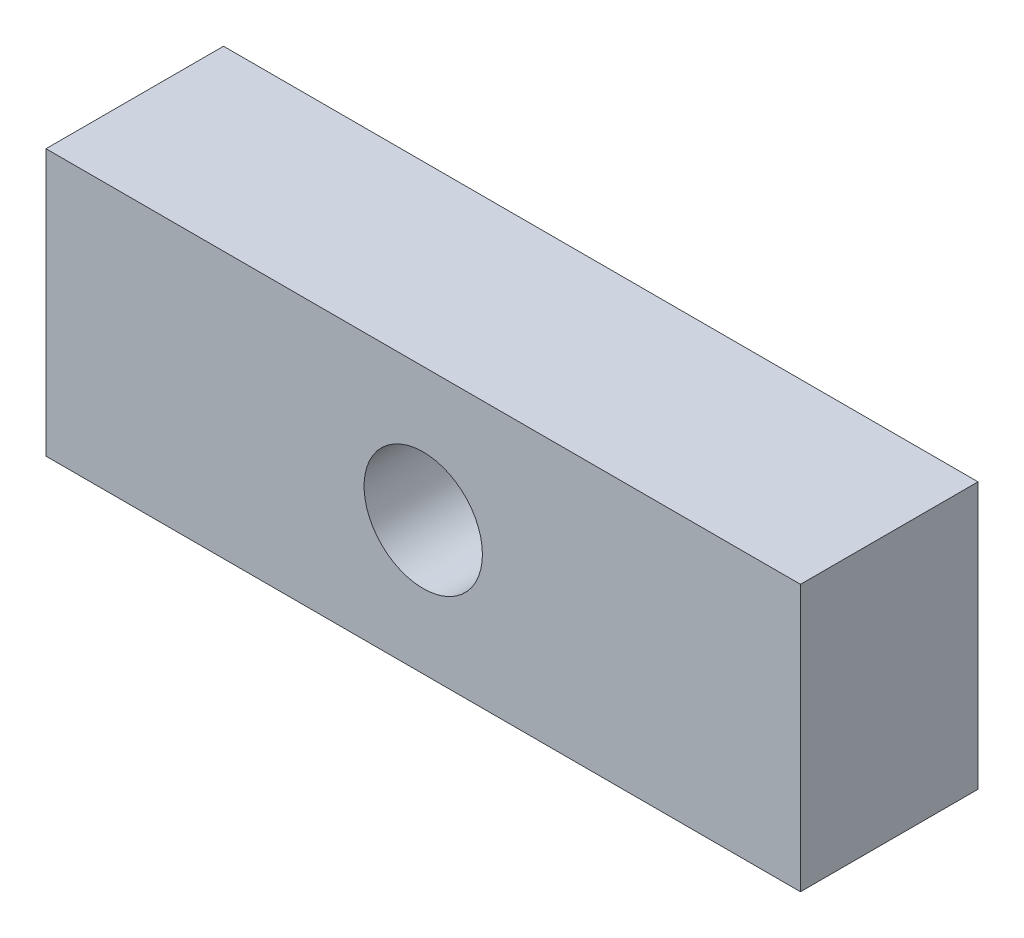
SolidWorks part; units mm, degrees
ref_plane "Front Plane" through (0, 0, 0) normal (0, 0, 1) x (1, 0, 0)
ref_plane "Top Plane" through (0, 0, 0) normal (0, 1, 0) x (1, 0, 0)
ref_plane "Right Plane" through (0, 0, 0) normal (1, 0, 0) x (0, 0, -1)
sketch "Sketch1" plane through (0, 0, 0) normal (0, 0, 1) x (1, 0, 0)
  line L1 (0, 0) -> (12.75, 0)
  line L2 (0, 0) -> (0, -4.5)
  line L3 (0, -4.5) -> (12.75, -4.5)
  line L4 (12.75, 0) -> (12.75, -4.5)
  dimension "D1" = 12.75
  dimension "D2" = 4.5
extrude "Boss-Extrude1" add sketch "Sketch1" along normal blind 3
sketch "Sketch2" plane through (0, 0, 3) normal (0, 0, 1) x (1, 0, 0)
  line L0 (0, -4.5) -> (12.75, -4.5) construction
  line L1 (0, 0) -> (0, -4.5) construction
  circle A0 centre (6.375, -2.25) radius 1
  dimension "D1" = 2
  dimension "D2" = 2.25
  dimension "D3" = 6.375
extrude "Cut-Extrude1" cut sketch "Sketch2" against normal blind 3
